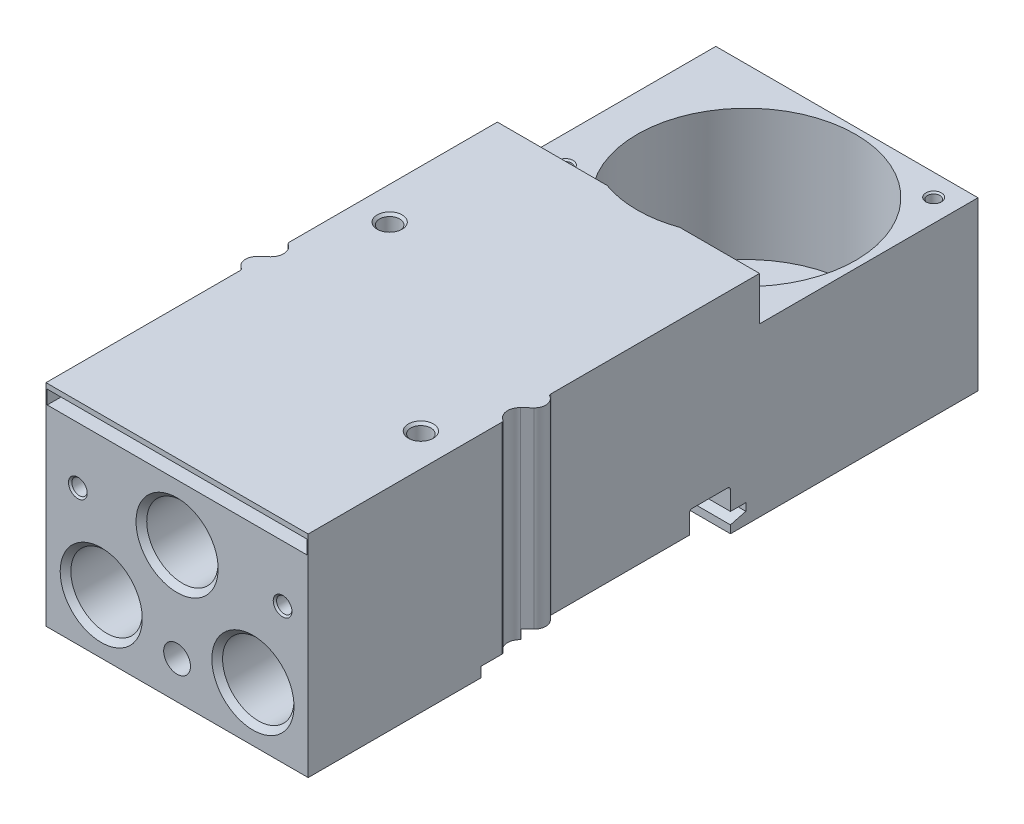
SolidWorks part; units mm, degrees
ref_plane "Front Plane" through (0, 0, 0) normal (0, 0, 1) x (1, 0, 0)
ref_plane "Top Plane" through (0, 0, 0) normal (0, 1, 0) x (1, 0, 0)
ref_plane "Right Plane" through (0, 0, 0) normal (1, 0, 0) x (0, 0, -1)
ref_plane "Plane1" through (0, 1.3, 0) normal (0, 1, 0) x (1, 0, 0)
sketch "Sketch1" plane through (0, 1.3, 0) normal (0, 1, 0) x (1, 0, 0)
  line L0 (-21, -22.5419) -> (-21, -53.65)
  line L1 (-21, -53.65) -> (21, -53.65)
  line L2 (21, -53.65) -> (21, -22.6542)
  line L3 (20.4839, -19.0892) -> (21.5795, -18.0647)
  line L4 (21, -14.7581) -> (21, 53.65)
  line L5 (21, 53.65) -> (-21, 53.65)
  line L6 (-21, 53.65) -> (-21, -14.6458)
  line L7 (-20.4839, -18.2108) -> (-21.5795, -19.2353)
  arc A0 (-21.5795, -19.2353) -> (-21.25, -22.1088) centre (-20.35, -20.55) ccw
  arc A1 (-21.25, -22.1088) -> (-21, -22.5419) centre (-21.5, -22.5419) cw
  arc A2 (21, -22.6542) -> (20.77, -22.2333) centre (20.5, -22.6542) ccw
  arc A3 (20.77, -22.2333) -> (20.4839, -19.0892) centre (21.85, -20.55) cw
  arc A4 (21.5795, -18.0647) -> (21.25, -15.1912) centre (20.35, -16.75) ccw
  arc A5 (21.25, -15.1912) -> (21, -14.7581) centre (21.5, -14.7581) cw
  arc A6 (-21, -14.6458) -> (-20.77, -15.0667) centre (-20.5, -14.6458) ccw
  arc A7 (-20.77, -15.0667) -> (-20.4839, -18.2108) centre (-21.85, -16.75) cw
extrude "Boss-Extrude1" add sketch "Sketch1" along normal blind 33.8
ref_plane "Plane2" through (0, 0, 0) normal (1, 0, 0) x (0, 0, -1)
sketch "Sketch2" plane through (0, 0, 0) normal (1, 0, 0) x (0, 0, -1)
  line L0 (-26, 2.9) -> (-26, -8.1744)
  line L1 (-26, -8.1744) -> (14, -7.9637)
  line L2 (14, -7.9637) -> (14, 2.5435)
  line L3 (14, 2.5435) -> (16.45, 3.2)
  line L4 (16.45, 3.2) -> (16.45, 4.4)
  line L5 (16.45, 4.4) -> (14, 4.4)
  line L6 (14, 4.4) -> (14, 7.4)
  line L7 (13.5, 7.9) -> (7.9, 7.9)
  line L8 (7.4, 7.4) -> (7.4, 4.4)
  line L9 (7.4, 4.4) -> (-19.05, 4.4)
  line L10 (-19.05, 4.4) -> (-19.05, 2.9)
  line L11 (-19.05, 2.9) -> (-26, 2.9)
  arc A0 (14, 7.4) -> (13.5, 7.9) centre (13.5, 7.4) ccw
  arc A1 (7.9, 7.9) -> (7.4, 7.4) centre (7.9, 7.4) ccw
extrude "Cut-Extrude1" cut sketch "Sketch2" against normal blind 25 and the other way blind 25
ref_plane "Plane3" through (0, 35.1, 0) normal (0, 1, 0) x (1, 0, 0)
sketch "Sketch3" plane through (0, 35.1, 0) normal (0, 1, 0) x (1, 0, 0)
  line L0 (-21, 18.65) -> (21, 18.65)
  line L1 (21, 18.65) -> (21, 53.65)
  line L2 (21, 53.65) -> (-21, 53.65)
  line L3 (-21, 53.65) -> (-21, 18.65)
extrude "Cut-Extrude2" cut sketch "Sketch3" against normal blind 7
ref_plane "Plane4" through (0, 10.05, 0) normal (0, 1, 0) x (1, 0, 0)
sketch "Sketch4" plane through (0, 10.05, 0) normal (0, 1, 0) x (1, 0, 0)
  line L0 (-12.15, -43.922) -> (-6.4275, -43.922)
  line L1 (-6.4275, -43.922) -> (-6.4275, -52.794)
  line L2 (-6.4275, -52.794) -> (-5.5715, -53.65)
  line L3 (-5.5715, -53.65) -> (-12.15, -53.65)
  line L4 (-12.15, -53.65) -> (-12.15, -43.922)
  line L5 (-12.15, -53.65) -> (-12.15, -43.922) construction
revolve "Cut-Revolve1" cut sketch "Sketch4" angle 360 about L5
cosmetic thread "Cosmetic Thread1" parameters "D1"=9.728, "D2"=13.157
ref_plane "Plane5" through (0, 10.05, 0) normal (0, 1, 0) x (1, 0, 0)
sketch "Sketch5" plane through (0, 10.05, 0) normal (0, 1, 0) x (1, 0, 0)
  line L0 (12.15, -43.922) -> (17.8725, -43.922)
  line L1 (17.8725, -43.922) -> (17.8725, -52.794)
  line L2 (17.8725, -52.794) -> (18.7285, -53.65)
  line L3 (18.7285, -53.65) -> (12.15, -53.65)
  line L4 (12.15, -53.65) -> (12.15, -43.922)
  line L5 (12.15, -53.65) -> (12.15, -43.922) construction
revolve "Cut-Revolve2" cut sketch "Sketch5" angle 360 about L5
cosmetic thread "Cosmetic Thread2" parameters "D1"=9.728, "D2"=13.157
ref_plane "Plane6" through (0, 23.05, 0) normal (0, 1, 0) x (1, 0, 0)
sketch "Sketch6" plane through (0, 23.05, 0) normal (0, 1, 0) x (1, 0, 0)
  line L0 (0, -43.922) -> (5.7225, -43.922)
  line L1 (5.7225, -43.922) -> (5.7225, -52.794)
  line L2 (5.7225, -52.794) -> (6.5785, -53.65)
  line L3 (6.5785, -53.65) -> (0, -53.65)
  line L4 (0, -53.65) -> (0, -43.922)
  line L5 (0, -53.65) -> (0, -43.922) construction
revolve "Cut-Revolve3" cut sketch "Sketch6" angle 360 about L5
cosmetic thread "Cosmetic Thread3" parameters "D1"=9.728, "D2"=13.157
ref_plane "Plane7" through (-15.75, 0, 0) normal (1, 0, 0) x (0, 0, -1)
sketch "Sketch7" plane through (-15.75, 0, 0) normal (1, 0, 0) x (0, 0, -1)
  line L0 (-3.85, 27.1) -> (-5.471, 27.1)
  line L1 (-5.471, 27.1) -> (-5.471, 34.721)
  line L2 (-5.471, 34.721) -> (-5.85, 35.1)
  line L3 (-5.85, 35.1) -> (-3.85, 35.1)
  line L4 (-3.85, 35.1) -> (-3.85, 27.1)
  line L5 (-3.85, 35.1) -> (-3.85, 27.1) construction
revolve "Cut-Revolve4" cut sketch "Sketch7" angle 360 about L5
cosmetic thread "Cosmetic Thread4" parameters "D1"=8, "D2"=4
ref_plane "Plane8" through (15.75, 0, 0) normal (1, 0, 0) x (0, 0, -1)
sketch "Sketch8" plane through (15.75, 0, 0) normal (1, 0, 0) x (0, 0, -1)
  line L0 (-30.35, 27.1) -> (-31.971, 27.1)
  line L1 (-31.971, 27.1) -> (-31.971, 34.721)
  line L2 (-31.971, 34.721) -> (-32.35, 35.1)
  line L3 (-32.35, 35.1) -> (-30.35, 35.1)
  line L4 (-30.35, 35.1) -> (-30.35, 27.1)
  line L5 (-30.35, 35.1) -> (-30.35, 27.1) construction
revolve "Cut-Revolve5" cut sketch "Sketch8" angle 360 about L5
cosmetic thread "Cosmetic Thread5" parameters "D1"=8, "D2"=4
ref_plane "Plane9" through (0, 35.1, 0) normal (0, 1, 0) x (1, 0, 0)
sketch "Sketch9" plane through (0, 35.1, 0) normal (0, 1, 0) x (1, 0, 0)
  circle A0 centre (2.4, 35.15) radius 17.5
extrude "Cut-Extrude3" cut sketch "Sketch9" against normal blind 28
ref_plane "Plane10" through (0, 23.05, 0) normal (0, 1, 0) x (1, 0, 0)
sketch "Sketch10" plane through (0, 23.05, 0) normal (0, 1, 0) x (1, 0, 0)
  line L0 (-15.9, -42.65) -> (-14.6705, -43.3599)
  line L1 (-14.6705, -43.3599) -> (-14.6705, -53.3795)
  line L2 (-14.6705, -53.3795) -> (-14.4, -53.65)
  line L3 (-14.4, -53.65) -> (-15.9, -53.65)
  line L4 (-15.9, -53.65) -> (-15.9, -42.65)
  line L5 (-15.9, -53.65) -> (-15.9, -42.65) construction
revolve "Cut-Revolve6" cut sketch "Sketch10" angle 360 about L5
cosmetic thread "Cosmetic Thread6" parameters "D1"=9, "D2"=3
ref_plane "Plane11" through (0, 23.05, 0) normal (0, 1, 0) x (1, 0, 0)
sketch "Sketch11" plane through (0, 23.05, 0) normal (0, 1, 0) x (1, 0, 0)
  line L0 (16.9, -42.65) -> (18.1295, -43.3599)
  line L1 (18.1295, -43.3599) -> (18.1295, -53.3795)
  line L2 (18.1295, -53.3795) -> (18.4, -53.65)
  line L3 (18.4, -53.65) -> (16.9, -53.65)
  line L4 (16.9, -53.65) -> (16.9, -42.65)
  line L5 (16.9, -53.65) -> (16.9, -42.65) construction
revolve "Cut-Revolve7" cut sketch "Sketch11" angle 360 about L5
cosmetic thread "Cosmetic Thread7" parameters "D1"=9, "D2"=3
ref_plane "Plane12" through (0, 0, 53.65) normal (0, 0, 1) x (1, 0, 0)
sketch "Sketch12" plane through (0, 0, 53.65) normal (0, 0, 1) x (1, 0, 0)
  line L0 (-20.8, 32.1) -> (20.8, 32.1)
  line L1 (20.8, 32.1) -> (20.8, 34.3)
  line L2 (20.8, 34.3) -> (-20.8, 34.3)
  line L3 (-20.8, 34.3) -> (-20.8, 32.1)
extrude "Cut-Extrude4" cut sketch "Sketch12" against normal blind 10
ref_plane "Plane13" through (0, 0, 0) normal (1, 0, 0) x (0, 0, -1)
sketch "Sketch13" plane through (0, 0, 0) normal (1, 0, 0) x (0, 0, -1)
  line L0 (-53.65, 7.3) -> (-53.65, 9.45)
  line L1 (-53.65, 9.45) -> (-43.65, 9.45)
  line L2 (-43.65, 9.45) -> (-43.65, 7.3)
  line L3 (-43.65, 7.3) -> (-53.65, 7.3)
  line L4 (-43.65, 7.3) -> (-53.65, 7.3) construction
revolve "Cut-Revolve8" cut sketch "Sketch13" angle 360 about L4
ref_plane "Plane14" through (17.4, 0, 0) normal (1, 0, 0) x (0, 0, -1)
sketch "Sketch14" plane through (17.4, 0, 0) normal (1, 0, 0) x (0, 0, -1)
  line L0 (50.15, 22.1) -> (49.1435, 22.1)
  line L1 (49.1435, 22.1) -> (49.1435, 27.8565)
  line L2 (49.1435, 27.8565) -> (48.9, 28.1)
  line L3 (48.9, 28.1) -> (50.15, 28.1)
  line L4 (50.15, 28.1) -> (50.15, 22.1)
  line L5 (50.15, 28.1) -> (50.15, 22.1) construction
revolve "Cut-Revolve9" cut sketch "Sketch14" angle 360 about L5
cosmetic thread "Cosmetic Thread8" parameters "D1"=6, "D2"=2.5
ref_plane "Plane15" through (-16.6, 0, 0) normal (1, 0, 0) x (0, 0, -1)
sketch "Sketch15" plane through (-16.6, 0, 0) normal (1, 0, 0) x (0, 0, -1)
  line L0 (25.15, 22.1) -> (24.1435, 22.1)
  line L1 (24.1435, 22.1) -> (24.1435, 27.8565)
  line L2 (24.1435, 27.8565) -> (23.9, 28.1)
  line L3 (23.9, 28.1) -> (25.15, 28.1)
  line L4 (25.15, 28.1) -> (25.15, 22.1)
  line L5 (25.15, 28.1) -> (25.15, 22.1) construction
revolve "Cut-Revolve10" cut sketch "Sketch15" angle 360 about L5
cosmetic thread "Cosmetic Thread9" parameters "D1"=6, "D2"=2.5
ref_plane "Plane16" through (0, 13, 0) normal (0, 1, 0) x (1, 0, 0)
sketch "Sketch16" plane through (0, 13, 0) normal (0, 1, 0) x (1, 0, 0)
  line L0 (-16.4, 53.65) -> (-14.525, 53.65)
  line L1 (-14.525, 53.65) -> (-15.025, 53.15)
  line L2 (-15.025, 53.15) -> (-15.025, 44.65)
  line L3 (-15.025, 44.65) -> (-16.4, 44.65)
  line L4 (-16.4, 44.65) -> (-16.4, 53.65)
  line L5 (-16.4, 44.65) -> (-16.4, 53.65) construction
revolve "Cut-Revolve11" cut sketch "Sketch16" angle 360 about L5
ref_plane "Plane17" through (0, 13, 0) normal (0, 1, 0) x (1, 0, 0)
sketch "Sketch17" plane through (0, 13, 0) normal (0, 1, 0) x (1, 0, 0)
  line L0 (16.4, 53.65) -> (18.275, 53.65)
  line L1 (18.275, 53.65) -> (17.775, 53.15)
  line L2 (17.775, 53.15) -> (17.775, 44.65)
  line L3 (17.775, 44.65) -> (16.4, 44.65)
  line L4 (16.4, 44.65) -> (16.4, 53.65)
  line L5 (16.4, 44.65) -> (16.4, 53.65) construction
revolve "Cut-Revolve12" cut sketch "Sketch17" angle 360 about L5
